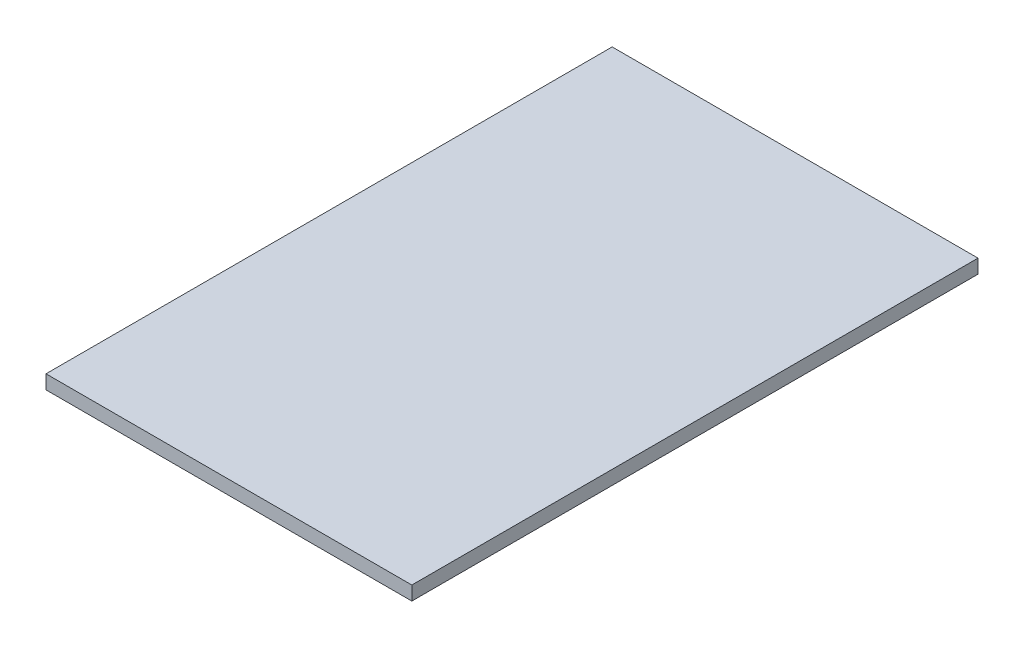
SolidWorks part; units mm, degrees
ref_plane "Front Plane" through (0, 0, 0) normal (0, 0, 1) x (1, 0, 0)
ref_plane "Top Plane" through (0, 0, 0) normal (0, 1, 0) x (1, 0, 0)
ref_plane "Right Plane" through (0, 0, 0) normal (1, 0, 0) x (0, 0, -1)
sketch "Sketch1" plane through (0, 0, 0) normal (0, 0, 1) x (1, 0, 0)
  line L0 (-21, 0) -> (21, 0)
  line L1 (-21, 0) -> (-21, 1.6)
  line L2 (-21, 1.6) -> (21, 1.6)
  line L3 (21, 1.6) -> (21, 0)
  point P4 (0, 0)
extrude "Boss-Extrude1" add sketch "Sketch1" along normal blind 65
